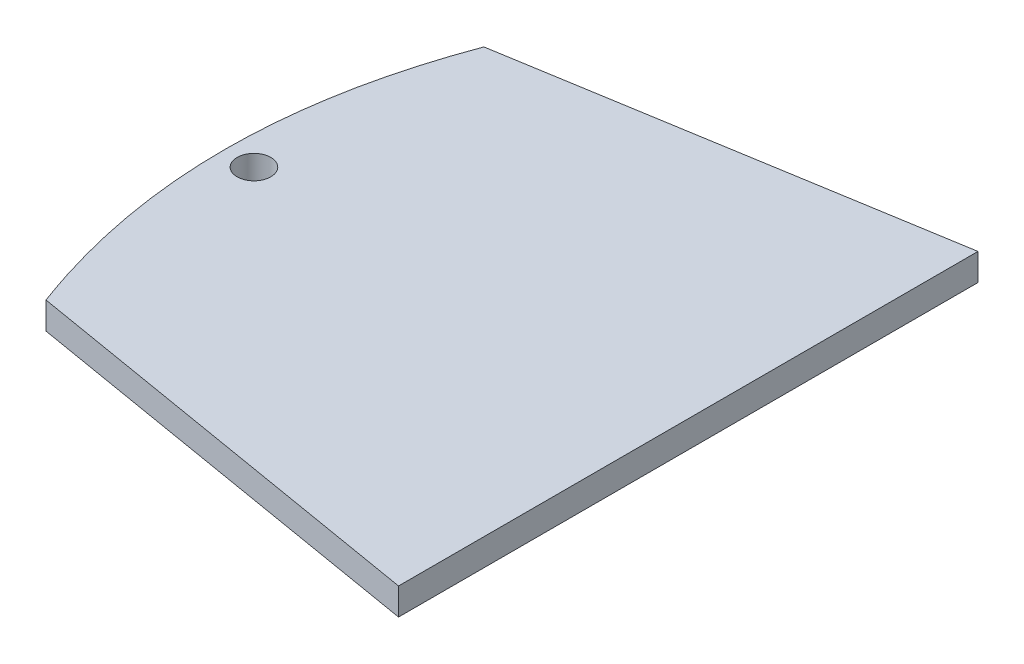
SolidWorks part; units mm, degrees
ref_plane "Alzado" through (0, 0, 0) normal (0, 0, 1) x (1, 0, 0)
ref_plane "Planta" through (0, 0, 0) normal (0, 1, 0) x (1, 0, 0)
ref_plane "Vista lateral" through (0, 0, 0) normal (1, 0, 0) x (0, 0, -1)
sketch "Croquis2" plane through (0, 0, 0) normal (0, 1, 0) x (1, 0, 0)
  line L0 (-79.6012, 51.5462) -> (-16.6517, 61.9292)
  line L1 (-16.6517, 61.9292) -> (-16.6517, -24.0708)
  line L2 (-16.6517, -24.0708) -> (-79.566, -13.4765)
  circle A0 centre (-81.2126, 19.0327) radius 2.5
  spline S0 degree 2 poles (-79.6012, 51.5462) (-91.7199, 19.0283) (-79.566, -13.4765) knots 0 0 0 1 1 1
  dimension "D1" = 5
extrude "Saliente-Extruir1" add sketch "Croquis2" along normal blind 4
